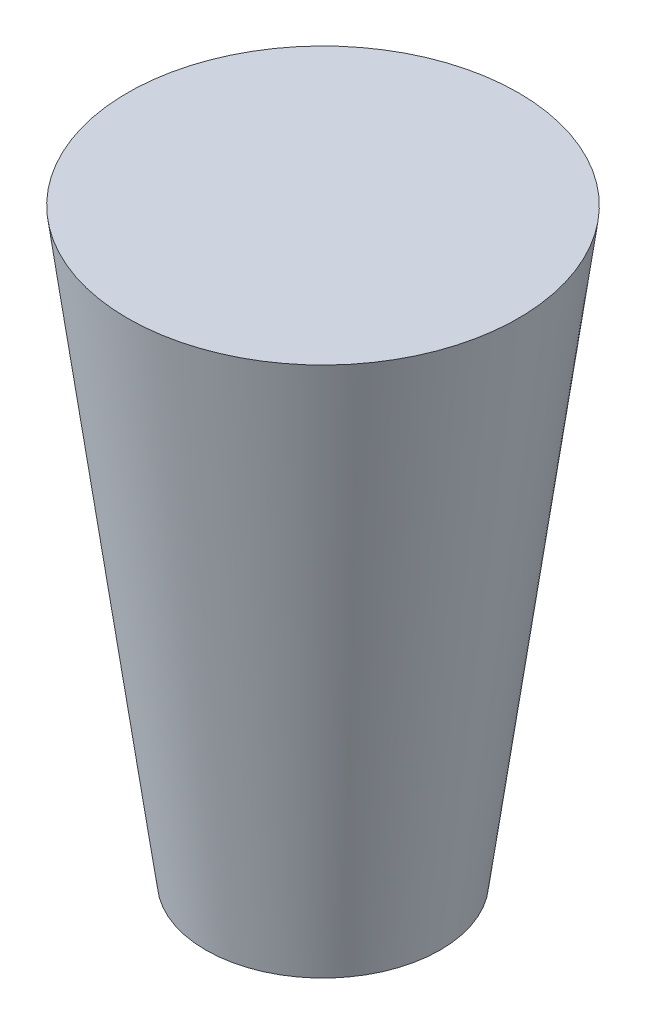
SolidWorks part; units mm, degrees
ref_plane "Plan de face" through (0, 0, 0) normal (0, 0, 1) x (1, 0, 0)
ref_plane "Plan de dessus" through (0, 0, 0) normal (0, 1, 0) x (1, 0, 0)
ref_plane "Plan de droite" through (0, 0, 0) normal (1, 0, 0) x (0, 0, -1)
sketch "Esquisse1" plane through (0, 0, 0) normal (0, 0, 1) x (1, 0, 0)
  line L0 (0, 112.0007) -> (0, -69.9403) construction
  line L1 (0, -50) -> (-30, -50)
  line L2 (-30, -50) -> (-50, 100)
  line L3 (-50, 100) -> (0, 100)
  line L4 (0, -50) -> (0, 100)
  dimension "D1" = 50
  dimension "D2" = 100
  dimension "D3" = 30
  dimension "D4" = 50
revolve "Révolution1" add sketch "Esquisse1" angle 360 about L0
